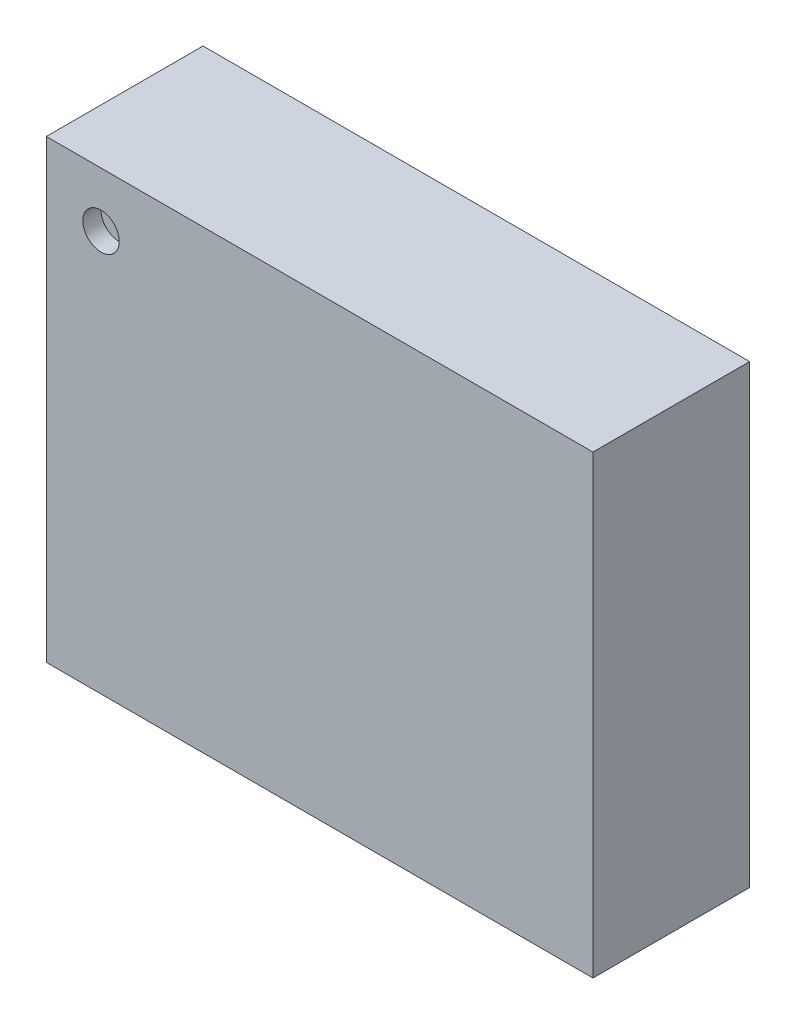
SolidWorks part; units mm, degrees
ref_plane "Front Plane" through (0, 0, 0) normal (0, 0, 1) x (1, 0, 0)
ref_plane "Top Plane" through (0, 0, 0) normal (0, 1, 0) x (1, 0, 0)
ref_plane "Right Plane" through (0, 0, 0) normal (1, 0, 0) x (0, 0, -1)
sketch "Sketch1" plane through (0, 0, 0) normal (0, 0, 1) x (1, 0, 0)
  line L1 (0, 0) -> (3, 0)
  line L2 (0, 0) -> (0, 2.5)
  line L3 (0, 2.5) -> (3, 2.5)
  line L4 (3, 0) -> (3, 2.5)
  dimension "D1" = 3
  dimension "D2" = 2.5
extrude "Boss-Extrude1" add sketch "Sketch1" along normal blind 0.86
sketch "Sketch2" plane through (0, 0, 0.86) normal (0, 0, 1) x (1, 0, 0)
  line L0 (0, 2.5) -> (0, 0) construction
  line L1 (3, 2.5) -> (0, 2.5) construction
  circle A0 centre (0.3, 2.2) radius 0.1
  dimension "D1" = 0.2
  dimension "D2" = 0.3
  dimension "D3" = 0.3
extrude "Cut-Extrude1" cut sketch "Sketch2" against normal blind 0.1
sketch "Sketch3" plane through (0, 0, 0) normal (0, 0, -1) x (-1, 0, 0)
  line L0 (-1.5, 2.5) -> (-1.5, 0) construction
  line L1 (-3, 2.5) -> (0, 2.5) construction
  line L2 (0, 0) -> (-3, 0) construction
  line L3 (-1, 2.4) -> (-1, 1.95) construction
  line L4 (-3, 0) -> (-3, 2.5) construction
  line L5 (-3, 1.25) -> (0, 1.25) construction
  line L6 (0, 2.5) -> (0, 0) construction
  line L7 (-1.125, 2.4) -> (-0.875, 2.4)
  line L8 (-1.125, 2.4) -> (-1.125, 1.95)
  line L9 (-1.125, 1.95) -> (-0.875, 1.95)
  line L10 (-0.875, 2.4) -> (-0.875, 1.95)
  line L11 (-1.625, 2.4) -> (-1.375, 2.4)
  line L12 (-1.625, 2.4) -> (-1.625, 1.95)
  line L13 (-1.625, 1.95) -> (-1.375, 1.95)
  line L14 (-1.375, 2.4) -> (-1.375, 1.95)
  line L15 (-2.125, 2.4) -> (-1.875, 2.4)
  line L16 (-2.125, 2.4) -> (-2.125, 1.95)
  line L17 (-2.125, 1.95) -> (-1.875, 1.95)
  line L18 (-1.875, 2.4) -> (-1.875, 1.95)
  line L19 (-1.875, 0.1) -> (-1.875, 0.55)
  line L20 (-2.125, 0.55) -> (-1.875, 0.55)
  line L21 (-2.125, 0.1) -> (-2.125, 0.55)
  line L22 (-2.125, 0.1) -> (-1.875, 0.1)
  line L23 (-1.375, 0.1) -> (-1.375, 0.55)
  line L24 (-1.625, 0.55) -> (-1.375, 0.55)
  line L25 (-1.625, 0.1) -> (-1.625, 0.55)
  line L26 (-1.625, 0.1) -> (-1.375, 0.1)
  line L27 (-0.875, 0.1) -> (-0.875, 0.55)
  line L28 (-1.125, 0.55) -> (-0.875, 0.55)
  line L29 (-1.125, 0.1) -> (-1.125, 0.55)
  line L30 (-1.125, 0.1) -> (-0.875, 0.1)
  line L31 (-2.9, 2) -> (-2.45, 2) construction
  line L32 (-2.9, 2.125) -> (-2.45, 2.125)
  line L33 (-2.9, 2.125) -> (-2.9, 1.875)
  line L34 (-2.9, 1.875) -> (-2.45, 1.875)
  line L35 (-2.45, 2.125) -> (-2.45, 1.875)
  line L36 (-2.9, 1.625) -> (-2.45, 1.625)
  line L37 (-2.9, 1.625) -> (-2.9, 1.375)
  line L38 (-2.9, 1.375) -> (-2.45, 1.375)
  line L39 (-2.45, 1.625) -> (-2.45, 1.375)
  line L40 (-2.9, 1.125) -> (-2.45, 1.125)
  line L41 (-2.9, 1.125) -> (-2.9, 0.875)
  line L42 (-2.9, 0.875) -> (-2.45, 0.875)
  line L43 (-2.45, 1.125) -> (-2.45, 0.875)
  line L44 (-2.9, 0.625) -> (-2.45, 0.625)
  line L45 (-2.9, 0.625) -> (-2.9, 0.375)
  line L46 (-2.9, 0.375) -> (-2.45, 0.375)
  line L47 (-2.45, 0.625) -> (-2.45, 0.375)
  line L48 (-0.55, 0.625) -> (-0.55, 0.375)
  line L49 (-0.1, 0.375) -> (-0.55, 0.375)
  line L50 (-0.1, 0.625) -> (-0.1, 0.375)
  line L51 (-0.1, 0.625) -> (-0.55, 0.625)
  line L52 (-0.55, 1.125) -> (-0.55, 0.875)
  line L53 (-0.1, 0.875) -> (-0.55, 0.875)
  line L54 (-0.1, 1.125) -> (-0.1, 0.875)
  line L55 (-0.1, 1.125) -> (-0.55, 1.125)
  line L56 (-0.55, 1.625) -> (-0.55, 1.375)
  line L57 (-0.1, 1.375) -> (-0.55, 1.375)
  line L58 (-0.1, 1.625) -> (-0.1, 1.375)
  line L59 (-0.1, 1.625) -> (-0.55, 1.625)
  line L60 (-0.55, 2.125) -> (-0.55, 2)
  line L61 (-0.1, 1.875) -> (-0.427, 1.875)
  line L62 (-0.1, 2.125) -> (-0.1, 1.875)
  line L63 (-0.1, 2.125) -> (-0.55, 2.125)
  line L64 (-0.55, 2) -> (-0.427, 1.875)
  dimension "D1" = 0.1
  dimension "D2" = 0.45
  dimension "D3" = 0.25
  dimension "D4" = 0.5
  dimension "D6" = 0.1
  dimension "D7" = 0.45
  dimension "D8" = 0.25
  dimension "D9" = 0.75
  dimension "D5" = 3
  dimension "D10" = 4
extrude "Boss-Extrude2" add sketch "Sketch3" along normal blind 0.05
